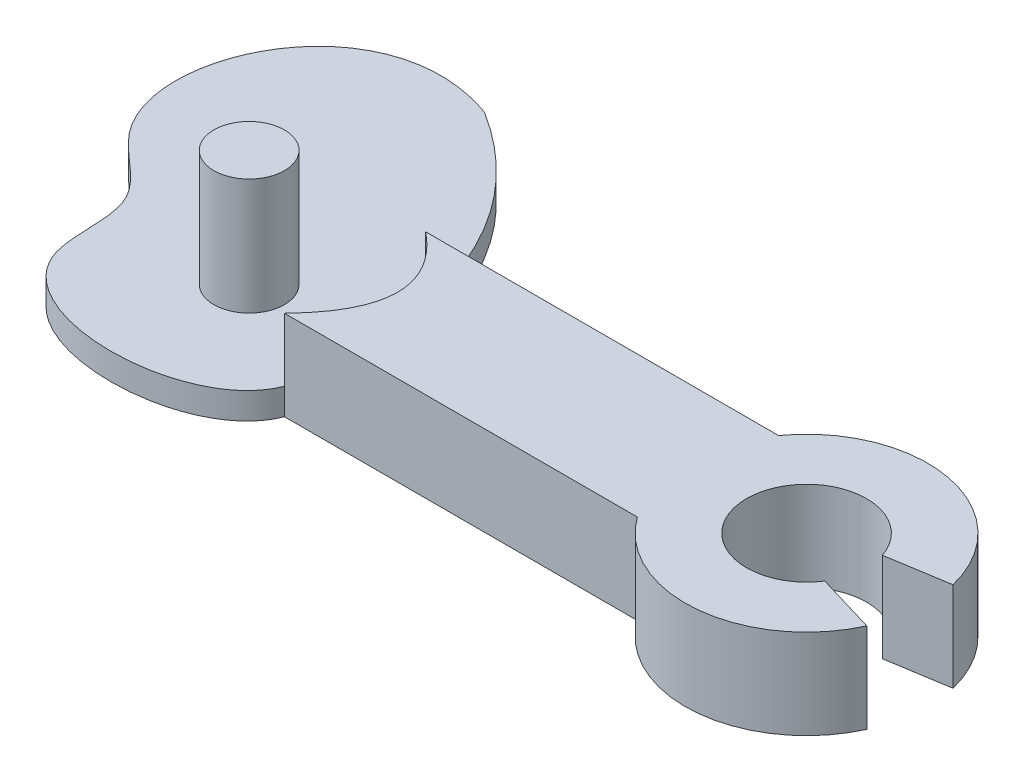
SolidWorks part; units mm, degrees
ref_plane "Front Plane" through (0, 0, 0) normal (0, 0, 1) x (1, 0, 0)
ref_plane "Top Plane" through (0, 0, 0) normal (0, 1, 0) x (1, 0, 0)
ref_plane "Right Plane" through (0, 0, 0) normal (1, 0, 0) x (0, 0, -1)
sketch "Sketch1" plane through (0, 0, 0) normal (0, 1, 0) x (1, 0, 0)
  line L0 (0, 0) -> (10, 0) construction
  line L1 (10, 0) -> (12.794, 0)
  line L2 (0, 0) -> (10, 0) construction
  line L3 (10, -2) -> (10, 2)
  line L4 (16.1332, 0.8101) -> (14.4086, 0.5319)
  line L5 (10, -2) -> (0, -2)
  line L6 (10, -2) -> (10, 2)
  line L7 (10, 2) -> (0, 2)
  line L8 (0, -2) -> (0, 2)
  line L9 (-6.5043, -2) -> (-0.5043, 2.6) construction
  line L10 (0, -2) -> (-6.5043, -2) construction
  line L11 (15.9224, -1.4212) -> (14.2261, -0.916)
  circle A0 centre (-3.5043, 0.3) radius 1 construction
  circle A1 centre (12.794, 0) radius 3.406 construction
  arc A2 (10, 2) -> (16.1332, 0.8101) centre (12.794, 0) cw
  arc A3 (10, -2) -> (15.9224, -1.4212) centre (12.794, 0) ccw
  circle A4 centre (12.794, 0) radius 1.7 construction
  arc A5 (14.2261, -0.916) -> (14.4169, 0.506) centre (12.794, 0) cw
  spline S0 degree 3 poles (0, -2) (-0.807, -4.0986) (-7.3608, -4.1963) (-6.3435, 0.5483) (-10.7782, 2.929) (-8.0517, 9.0455) (-3.8921, 7.5585) knots 0 0 0 0 0.35586 0.470048 0.583543 1 1 1 1
  spline S1 degree 2 poles (-3.8921, 7.5585) (-0.7715, 5.6017) (0, 2) knots 0 0 0 1 1 1
  point P6 (10, 0)
  dimension "D7" = 2
  dimension "D3" = 6.812
  dimension "D5" = 3.4
  dimension "D1" = 10
  dimension "D2" = 2.794
  dimension "D4" = 4
  dimension "D6" = 6
  dimension "D8" = 1.7468
extrude "Boss-Extrude2" add sketch "Sketch1" along normal blind 2.54 contours S1 S0 L8 | L8 L5 L3 L7 | L11 A5 L1 L3 A3 | L1 A5 L4 A2 L3
ref_plane "Plane1" through (0, 2.54, 0) normal (0, 1, 0) x (1, 0, 0)
sketch "Sketch3" plane through (0, 2.54, 0) normal (0, 1, 0) x (1, 0, 0)
  line L0 (0, 0) -> (-3, 0)
  circle A0 centre (-3, 0) radius 1
  dimension "D2" = 2
  dimension "D1" = 3
extrude "Boss-Extrude3" add sketch "Sketch3" along normal blind 1.5
ref_plane "Plane2" through (0, 0, 0) normal (0, -1, 0) x (-1, 0, 0)
sketch "Sketch4" plane through (0, 0, 0) normal (0, -1, 0) x (-1, 0, 0)
  line L0 (0, 0) -> (4.8724, 3.5013) construction
  line L2 (0, 0) -> (4.8724, 0) construction
  circle A0 centre (4.8724, 3.5013) radius 1
  dimension "D4" = 2
  dimension "D1" = 6
  dimension "D2" = 3.5013
  dimension "D3" = 35.701
extrude "Boss-Extrude5" add sketch "Sketch4" along normal blind 1.5 contours A0
ref_plane "Plane3" through (0, 2.02, 0) normal (0, 1, 0) x (1, 0, 0)
sketch "Sketch6" plane through (0, 2.02, 0) normal (0, 1, 0) x (1, 0, 0)
  line L0 (-3, 1) -> (-3, -1) construction
  line L1 (-4, 0) -> (-2, 0) construction
  line L2 (0, 8.8591) -> (0, 2)
  line L3 (-11.0926, 8.8591) -> (0, 8.8591)
  line L4 (-11.0926, 8.8591) -> (-11.0926, -4.6725)
  line L5 (-11.0926, -4.6725) -> (0, -4.6725)
  line L7 (0, -2) -> (0, -4.6725)
  circle A0 centre (-3, 0) radius 1 construction
  circle A1 centre (-3, 0) radius 1 construction
  circle A2 centre (-3, 0) radius 1
  spline S0 degree 2 poles (0, 2) (2.1752, 0.2382) (0, -2) knots 0 0 0 1 1 1
extrude "Cut-Extrude1" cut sketch "Sketch6" along normal blind 2.54 and the other way blind 1.27
